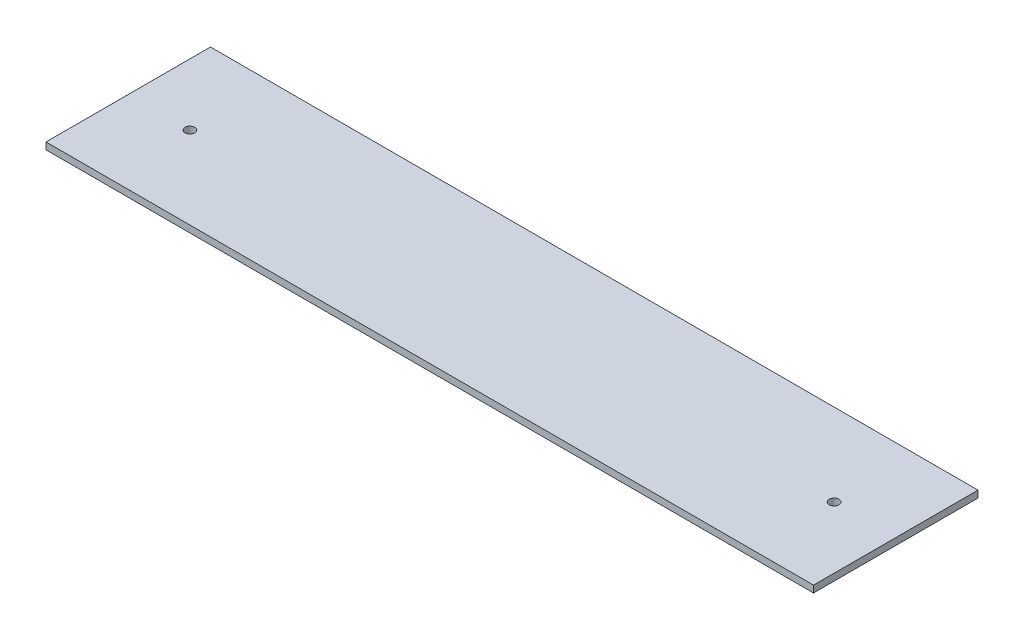
SolidWorks part; units mm, degrees
ref_plane "Front Plane" through (0, 0, 0) normal (0, 0, 1) x (1, 0, 0)
ref_plane "Top Plane" through (0, 0, 0) normal (0, 1, 0) x (1, 0, 0)
ref_plane "Right Plane" through (0, 0, 0) normal (1, 0, 0) x (0, 0, -1)
sketch "Sketch1" plane through (0, 0, 0) normal (0, 1, 0) x (1, 0, 0)
  line L1 (-177.8, -38.1) -> (177.8, -38.1)
  line L2 (-177.8, -38.1) -> (-177.8, 38.1)
  line L3 (-177.8, 38.1) -> (177.8, 38.1)
  line L4 (177.8, -38.1) -> (177.8, 38.1)
  line L5 (-177.8, -38.1) -> (177.8, 38.1) construction
  line L6 (-177.8, 38.1) -> (177.8, -38.1) construction
  circle A0 centre (-149.225, 0) radius 2.25
  circle A1 centre (149.225, 0) radius 2.25
  point P0 (0, 0)
  dimension "D7" = 4.5
  dimension "D8" = 4.5
  dimension "D1" = 76.2
  dimension "D2" = 355.6
  dimension "D3" = 38.1
  dimension "D4" = 38.1
  dimension "D5" = 28.575
  dimension "D6" = 28.575
extrude "Boss-Extrude1" add sketch "Sketch1" against normal blind 3.175 contours L2 L1 L4 L3
